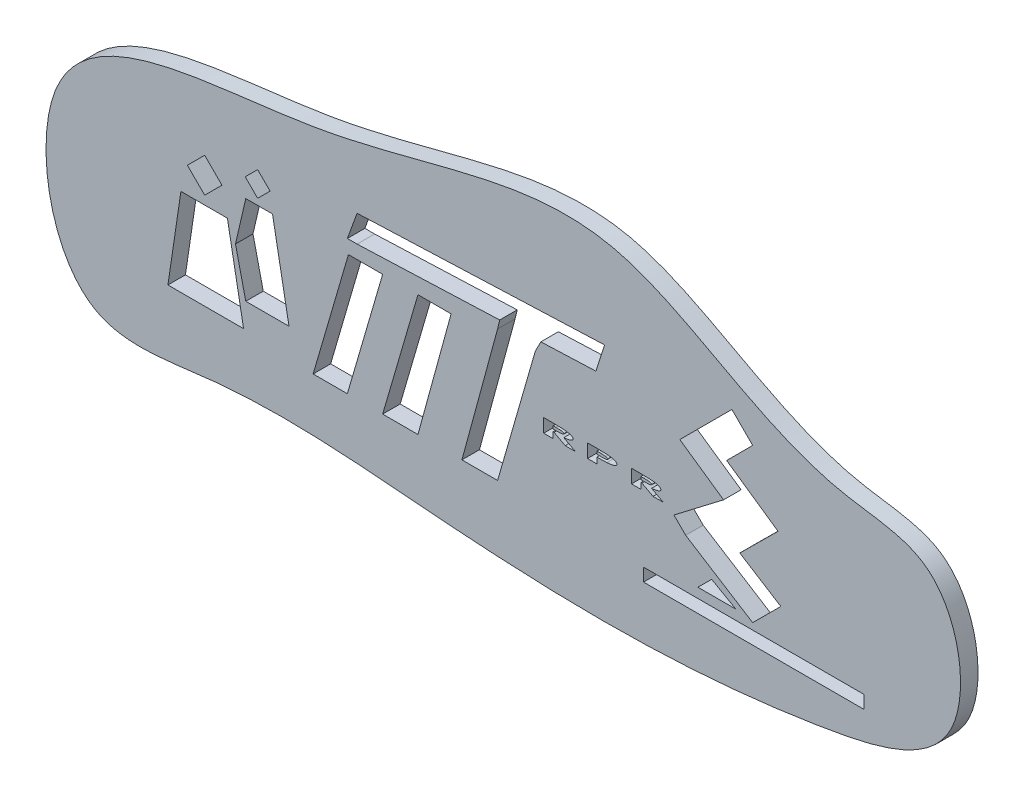
SolidWorks part; units mm, degrees
ref_plane "Front Plane" through (0, 0, 0) normal (0, 0, 1) x (1, 0, 0)
ref_plane "Top Plane" through (0, 0, 0) normal (0, 1, 0) x (1, 0, 0)
ref_plane "Right Plane" through (0, 0, 0) normal (1, 0, 0) x (0, 0, -1)
sketch "Sketch2" plane through (0, 0, 0) normal (0, 0, 1) x (1, 0, 0)
  spline S0 degree 3 poles (-77.8487, -2.7793) (7.5643, -5.7932) (74.8561, 26.7602) (121.1152, -14.8319) (165.0645, -15.1925) (172.1632, -60.1488) (105.4614, -75.1257) (43.9377, -72.9001) (-16.6432, -66.7183) (-65.6526, -76.7659) (-77.8487, -2.7793) (7.5643, -5.7932) (74.8561, 26.7602) knots -0.268212 -0.215088 -0.132289 0 0.146699 0.26417 0.306774 0.367882 0.435987 0.626986 0.731788 0.784912 0.867711 1 1.146699 1.26417 1.306774 only from (0, 0) to (0, 0)
extrude "Boss-Extrude2" add sketch "Sketch2" along normal blind 4.5174
sketch "Sketch5" plane through (0, 0, 4.5174) normal (0, 0, 1) x (1, 0, 0)
  line L0 (-37.4574, -54.1135) -> (-17.9397, -54.1135)
  line L1 (-17.9397, -54.1135) -> (-22.1221, -31.5287)
  line L3 (-37.4574, -54.1135) -> (-34.1115, -31.5287)
  line L4 (-34.1115, -31.5287) -> (-22.1221, -31.5287)
extrude "Cut-Extrude4" cut sketch "Sketch5" against normal blind 25.4
sketch "Sketch9" plane through (0, 0, 4.5174) normal (0, 0, 1) x (1, 0, 0)
  line L0 (-27.9774, -29.3171) -> (-32.4386, -24.8559)
  line L1 (-32.4386, -24.8559) -> (-27.9774, -20.3947)
  line L2 (-27.9774, -20.3947) -> (-23.5162, -24.8559)
  line L3 (-23.5162, -24.8559) -> (-27.9774, -29.3171)
extrude "Cut-Extrude9" cut sketch "Sketch9" against normal blind 25.4
sketch "Sketch10" plane through (0, 0, 4.5174) normal (0, 0, 1) x (1, 0, 0)
  line L0 (-17.3821, -47.7195) -> (-6.2291, -47.7195)
  line L1 (-6.2291, -47.7195) -> (-10.4799, -24.7653)
  line L2 (-10.4799, -24.7653) -> (-17.3821, -24.7653)
  line L3 (-17.3821, -24.7653) -> (-20.0309, -36.2424)
  line L4 (-20.0309, -36.2424) -> (-17.3821, -47.7195)
extrude "Cut-Extrude11" cut sketch "Sketch10" against normal blind 25.4
sketch "Sketch12" plane through (0, 0, 4.5174) normal (0, 0, 1) x (1, 0, 0)
  line L0 (-14.315, -23.183) -> (-17.5215, -19.9765)
  line L1 (-17.5215, -19.9765) -> (-14.315, -16.77)
  line L2 (-14.315, -16.77) -> (-11.1085, -19.9765)
  line L3 (-11.1085, -19.9765) -> (-14.315, -23.183)
extrude "Cut-Extrude12" cut sketch "Sketch12" against normal blind 25.4
sketch "Sketch13" plane through (0, 0, 4.5174) normal (0, 0, 1) x (1, 0, 0)
  line L1 (85.2253, -55.8054) -> (142.1055, -55.8054)
  line L2 (85.2253, -55.8054) -> (85.2253, -59.1513)
  line L3 (85.2253, -59.1513) -> (142.1055, -59.1513)
  line L4 (142.1055, -55.8054) -> (142.1055, -59.1513)
  line L5 (85.2253, -55.8054) -> (142.1055, -59.1513) construction
  line L6 (85.2253, -59.1513) -> (142.1055, -55.8054) construction
  point P0 (113.6654, -57.4784)
extrude "Cut-Extrude13" cut sketch "Sketch13" against normal blind 25.4
sketch "Sketch14" plane through (0, 0, 4.5174) normal (0, 0, 1) x (1, 0, 0)
  line L0 (113.3866, -54.1325) -> (120.636, -46.883)
  line L1 (120.636, -46.883) -> (110.0656, -40.2339)
  line L3 (113.3866, -54.1325) -> (96.0995, -43.2583)
  line L11 (96.0995, -43.2583) -> (93.075, -40.2339)
  line L12 (93.075, -40.2339) -> (105.8796, -30.4537)
  line L13 (105.8796, -30.4537) -> (94.5872, -22.6253)
  line L14 (94.5872, -22.6253) -> (108.0299, -9.1827)
  line L15 (108.0299, -9.1827) -> (113.3866, -14.5394)
  line L16 (113.3866, -14.5394) -> (106.6653, -21.2607)
  line L17 (106.6653, -21.2607) -> (119.9261, -30.4537)
  line L18 (119.9261, -30.4537) -> (110.0656, -40.2339)
extrude "Cut-Extrude14" cut sketch "Sketch14" against normal blind 25.4
sketch "Sketch15" plane through (0, 0, 4.5174) normal (0, 0, 1) x (1, 0, 0)
  line L0 (102.8033, -49.7381) -> (99.2576, -53.2838)
  line L1 (99.2576, -53.2838) -> (109.0438, -53.2838)
  line L2 (109.0438, -53.2838) -> (102.8033, -49.7381)
extrude "Cut-Extrude15" cut sketch "Sketch15" against normal blind 25.4
sketch "Sketch16" plane through (0, 0, 4.5174) normal (0, 0, 1) x (1, 0, 0)
  line L0 (11.3369, -13.7029) -> (75.1876, -11.1935)
  line L1 (75.1876, -11.1935) -> (72.957, -18.1641)
  line L2 (72.957, -18.1641) -> (11.3369, -20.5859)
  line L3 (11.3369, -20.5859) -> (8.8274, -20.5859)
  line L4 (8.8274, -20.5859) -> (11.3369, -13.7029)
extrude "Cut-Extrude16" cut sketch "Sketch16" against normal blind 68.326
sketch "Sketch17" plane through (0, 0, 4.5174) normal (0, 0, 1) x (1, 0, 0)
  line L0 (9.1063, -24.041) -> (0, -55.2694)
  line L1 (9.1063, -24.041) -> (17.9337, -24.041)
  line L2 (0, -55.2694) -> (8.8274, -55.2694)
  line L3 (17.9337, -24.041) -> (8.8274, -55.2694)
  line L4 (17.9337, -55.2694) -> (27.04, -24.041)
  line L8 (35.5946, -24.041) -> (27.04, -55.2694)
  line L9 (27.04, -55.2694) -> (17.9337, -55.2694)
  line L10 (27.04, -24.041) -> (35.5946, -24.041)
  line L11 (47.584, -21.4196) -> (57.3429, -21.4196)
  line L12 (57.3429, -21.4196) -> (47.584, -55.2694)
  line L14 (47.584, -21.4196) -> (38.3828, -55.2694)
  line L15 (38.3828, -55.2694) -> (47.584, -55.2694)
extrude "Cut-Extrude26" cut sketch "Sketch17" against normal blind 68.326
sketch "Sketch21" plane through (0, 0, 4.5174) normal (0, 0, 1) x (1, 0, 0)
  line L0 (48.1252, -19.1401) -> (58.737, -18.723)
  line L1 (11.3369, -20.5859) -> (72.957, -18.1641) construction
  line L2 (58.737, -18.723) -> (57.3429, -21.4196)
  line L3 (57.3429, -21.4196) -> (47.584, -21.4196)
  line L4 (47.584, -21.4196) -> (48.1252, -19.1401)
extrude "Cut-Extrude27" cut sketch "Sketch21" against normal blind 68.326
sketch "Sketch24" plane through (0, 0, 4.5174) normal (0, 0, 1) x (1, 0, 0)
  text T0 "RPR" font "Century Gothic" height 3.5
extrude "Cut-Extrude32" cut sketch "Sketch24" against normal blind 107.442
